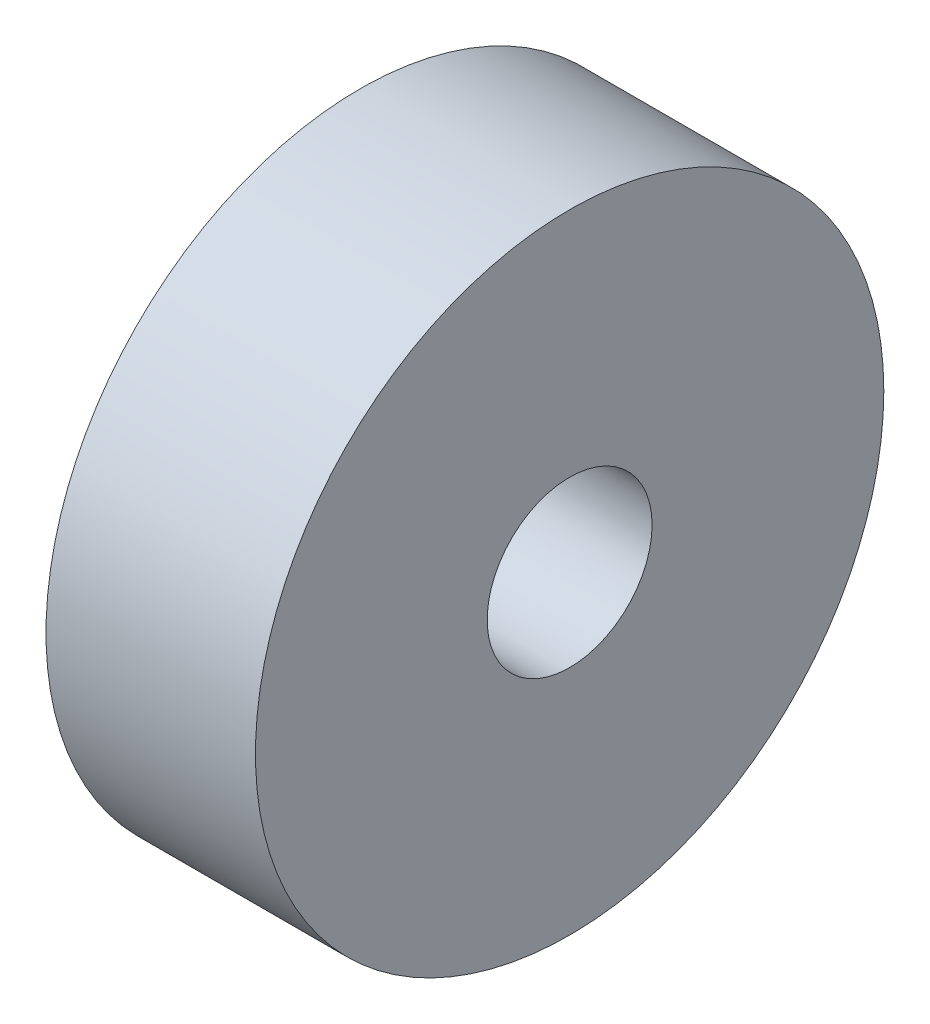
SolidWorks part; units mm, degrees
material "NEOPRENE"
ref_plane "Front Plane" through (0, 0, 0) normal (0, 0, 1) x (1, 0, 0)
ref_plane "Top Plane" through (0, 0, 0) normal (0, 1, 0) x (1, 0, 0)
ref_plane "Right Plane" through (0, 0, 0) normal (1, 0, 0) x (0, 0, -1)
sketch "Sketch1" plane through (0, 0, 0) normal (1, 0, 0) x (0, 0, -1)
  circle A0 centre (0, 0) radius 19.05
  circle A1 centre (0, 0) radius 5
  dimension "D1" = 38.1
  dimension "D2" = 10
extrude "Boss-Extrude1" add sketch "Sketch1" along normal blind 12.7
